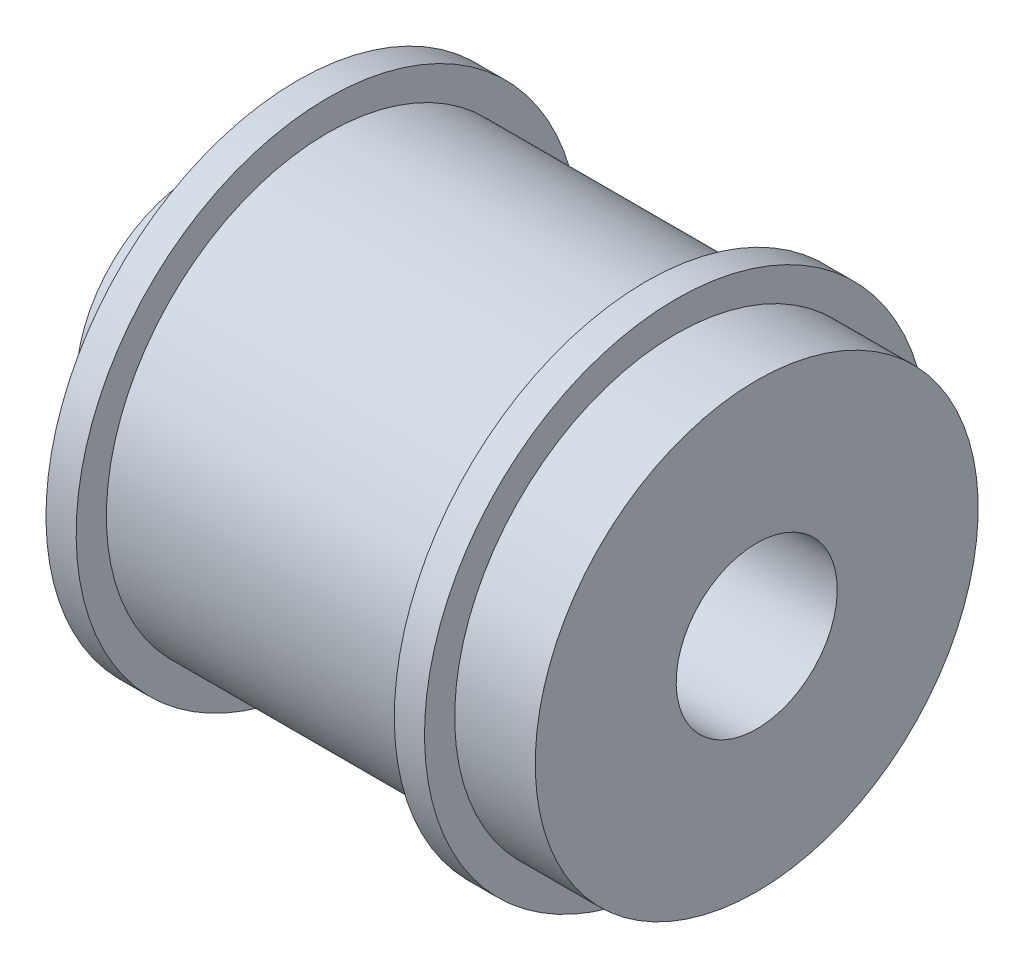
SolidWorks part; units mm, degrees
ref_plane "Front Plane" through (0, 0, 0) normal (0, 0, 1) x (1, 0, 0)
ref_plane "Top Plane" through (0, 0, 0) normal (0, 1, 0) x (1, 0, 0)
ref_plane "Right Plane" through (0, 0, 0) normal (1, 0, 0) x (0, 0, -1)
sketch "Sketch1" plane through (0, 0, 0) normal (0, 0, 1) x (1, 0, 0)
  line L1 (0, -55) -> (0, 55) construction
  line L2 (0, 11) -> (-4, 11)
  line L3 (-4, 11) -> (-4, 12.5)
  line L4 (-4, 12.5) -> (-5.5, 12.5)
  line L5 (-5.5, 12.5) -> (-5.5, 11)
  line L6 (-5.5, 11) -> (-21.3, 11)
  line L7 (-21.3, 11) -> (-21.3, 12.5)
  line L8 (-21.3, 12.5) -> (-22.8, 12.5)
  line L9 (-22.8, 12.5) -> (-22.8, 6)
  line L10 (-22.8, 6) -> (-27.8, 6)
  line L11 (-27.8, 6) -> (-27.8, 0)
  line L12 (55, 0) -> (-55, 0) construction
  line L15 (0, 11) -> (0, 4)
  line L16 (0, 4) -> (-9.7736, 4)
  line L17 (-9.7736, 4) -> (-9.7736, 0)
  line L18 (-9.7736, 0) -> (-27.8, 0)
  dimension "D1" = 11
  dimension "D2" = 12.5
  dimension "D3" = 11
  dimension "D4" = 1.5
  dimension "D5" = 18.8
  dimension "D6" = 4
  dimension "D7" = 6
  dimension "D8" = 5
  dimension "D9" = 4
revolve "Revolve1" add sketch "Sketch1" angle 360 about L18
